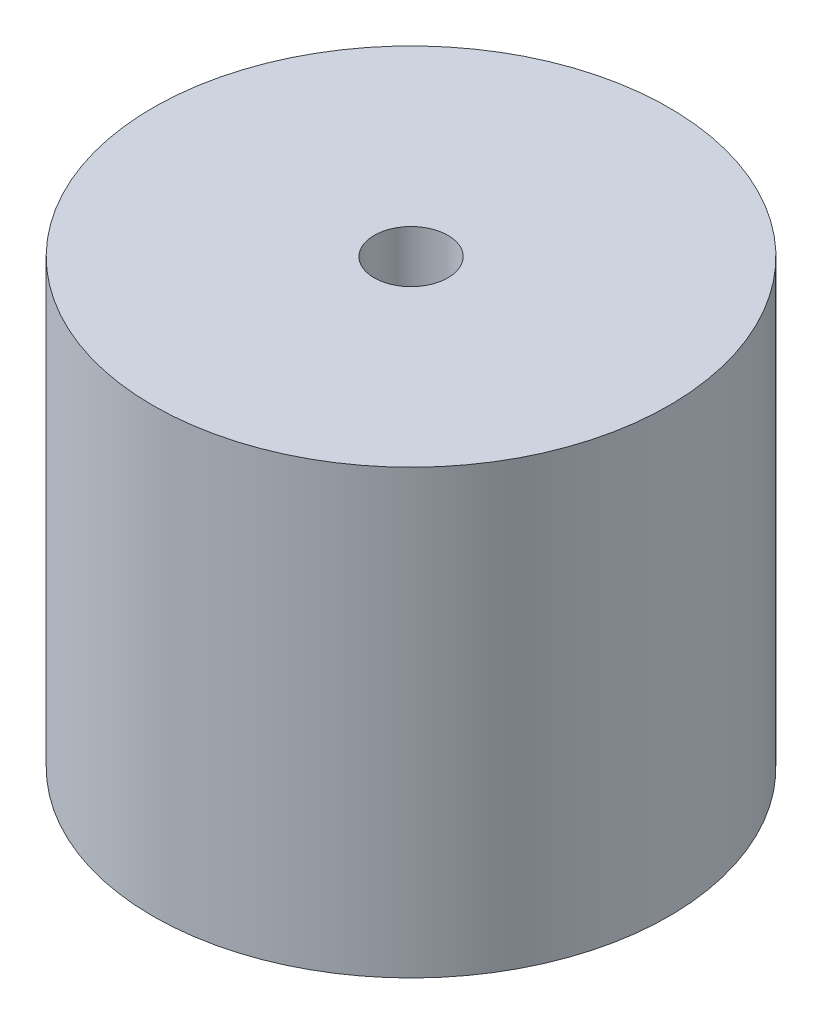
SolidWorks part; units mm, degrees
ref_plane "Front Plane" through (0, 0, 0) normal (0, 0, 1) x (1, 0, 0)
ref_plane "Top Plane" through (0, 0, 0) normal (0, 1, 0) x (1, 0, 0)
ref_plane "Right Plane" through (0, 0, 0) normal (1, 0, 0) x (0, 0, -1)
sketch "Sketch1" plane through (0, 0, 0) normal (0, 1, 0) x (1, 0, 0)
  circle A0 centre (0, 0) radius 22.225
  circle A1 centre (0, 0) radius 3.175
  dimension "D1" = 44.45
  dimension "D2" = 6.35
extrude "Boss-Extrude1" add sketch "Sketch1" along normal blind 38.1
